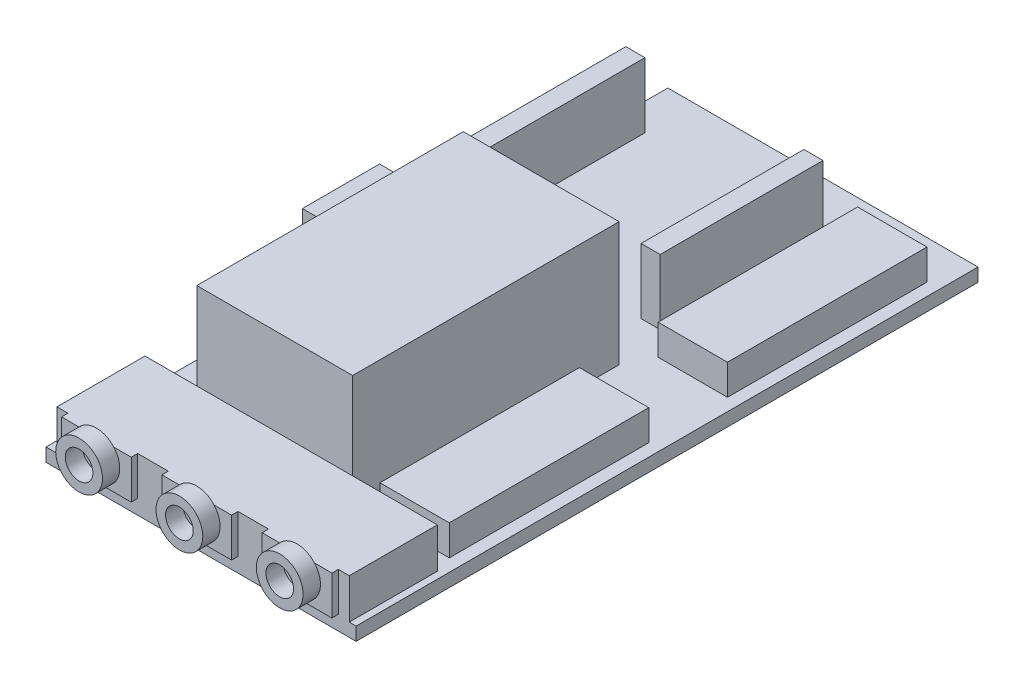
SolidWorks part; units mm, degrees
ref_plane "Front Plane" through (0, 0, 0) normal (0, 0, 1) x (1, 0, 0)
ref_plane "Top Plane" through (0, 0, 0) normal (0, 1, 0) x (1, 0, 0)
ref_plane "Right Plane" through (0, 0, 0) normal (1, 0, 0) x (0, 0, -1)
sketch "Sketch1" plane through (0, 0, 0) normal (0, 1, 0) x (1, 0, 0)
  line L1 (-19.9, -39.9) -> (19.9, -39.9)
  line L2 (-19.9, -39.9) -> (-19.9, 39.9)
  line L3 (-19.9, 39.9) -> (19.9, 39.9)
  line L4 (19.9, -39.9) -> (19.9, 39.9)
  line L5 (-19.9, -39.9) -> (19.9, 39.9) construction
  line L6 (-19.9, 39.9) -> (19.9, -39.9) construction
  point P0 (0, 0)
  dimension "D1" = 39.8
  dimension "D2" = 79.8
extrude "Boss-Extrude1" add sketch "Sketch1" along normal blind 1.7
sketch "Sketch2" plane through (0, 1.7, 0) normal (0, 1, 0) x (1, 0, 0)
  line L0 (-19.9, 39.9) -> (-19.9, -39.9) construction
  line L1 (-12.27, -28.18) -> (7.73, -28.18)
  line L2 (-12.27, -28.18) -> (-12.27, 6.02)
  line L3 (-12.27, 6.02) -> (7.73, 6.02)
  line L4 (7.73, -28.18) -> (7.73, 6.02)
  line L5 (-12.27, -28.18) -> (7.73, 6.02) construction
  line L6 (-12.27, 6.02) -> (7.73, -28.18) construction
  line L7 (19.9, 39.9) -> (-19.9, 39.9) construction
  point P0 (-2.27, -11.08)
  dimension "D1" = 34.2
  dimension "D2" = 20
  dimension "D3" = 7.63
  dimension "D4" = 33.88
extrude "Boss-Extrude2" add sketch "Sketch2" along normal blind 15.9
sketch "Sketch3" plane through (0, 1.7, 0) normal (0, 1, 0) x (1, 0, 0)
  line L0 (-19.9, 39.9) -> (-19.9, -39.9) construction
  line L1 (-18.84, 12.55) -> (-16.39, 12.55)
  line L2 (-18.84, 12.55) -> (-18.84, 33.45)
  line L3 (-18.84, 33.45) -> (-16.39, 33.45)
  line L4 (-16.39, 12.55) -> (-16.39, 33.45)
  line L5 (4.01, 12.55) -> (6.46, 12.55)
  line L6 (4.01, 12.55) -> (4.01, 33.45)
  line L7 (4.01, 33.45) -> (6.46, 33.45)
  line L8 (6.46, 12.55) -> (6.46, 33.45)
  line L9 (19.9, 39.9) -> (-19.9, 39.9) construction
  dimension "D1" = 20.9
  dimension "D2" = 2.45
  dimension "D3" = 2.45
  dimension "D4" = 20.4
  dimension "D5" = 1.06
  dimension "D6" = 6.45
extrude "Boss-Extrude3" add sketch "Sketch3" along normal blind 8.35
sketch "Sketch4" plane through (0, 1.7, 0) normal (0, 1, 0) x (1, 0, 0)
  line L1 (-19.9, -7) -> (-12.27, -7)
  line L2 (-19.9, -7) -> (-19.9, 2.9)
  line L3 (-19.9, 2.9) -> (-12.27, 2.9)
  line L4 (-12.27, -7) -> (-12.27, 2.9)
  line L5 (-19.9, 39.9) -> (-19.9, -39.9) construction
  line L6 (-12.27, 6.02) -> (-12.27, -28.18) construction
  line L7 (19.9, 39.9) -> (-19.9, 39.9) construction
  dimension "D1" = 9.9
  dimension "D2" = 37
extrude "Boss-Extrude4" add sketch "Sketch4" along normal blind 10.05
sketch "Sketch5" plane through (0, 1.7, 0) normal (0, 1, 0) x (1, 0, 0)
  line L0 (19.9, 39.9) -> (-19.9, 39.9) construction
  line L1 (9.4, -26.35) -> (18.3, -26.35)
  line L2 (9.4, -26.35) -> (9.4, -0.75)
  line L3 (9.4, -0.75) -> (18.3, -0.75)
  line L4 (18.3, -26.35) -> (18.3, -0.75)
  line L5 (9.4, 9.35) -> (18.3, 9.35)
  line L6 (9.4, 9.35) -> (9.4, 34.95)
  line L7 (9.4, 34.95) -> (18.3, 34.95)
  line L8 (18.3, 9.35) -> (18.3, 34.95)
  line L9 (19.9, -39.9) -> (19.9, 39.9) construction
  dimension "D1" = 8.9
  dimension "D2" = 25.6
  dimension "D3" = 10.1
  dimension "D4" = 4.95
  dimension "D5" = 25.6
  dimension "D6" = 1.6
extrude "Boss-Extrude5" add sketch "Sketch5" along normal blind 3.9
sketch "Sketch6" plane through (0, 1.7, 0) normal (0, 1, 0) x (1, 0, 0)
  line L0 (-19.9, -7) -> (-19.9, -39.9) construction
  line L1 (-18.5, -28.6) -> (19.02, -28.6)
  line L2 (-18.5, -28.6) -> (-18.5, -39.9)
  line L3 (-18.5, -39.9) -> (19.02, -39.9)
  line L4 (19.02, -28.6) -> (19.02, -39.9)
  line L5 (19.9, -39.9) -> (19.9, 39.9) construction
  line L6 (-19.9, -39.9) -> (19.9, -39.9) construction
  dimension "D1" = 37.52
  dimension "D2" = 1.4
  dimension "D3" = 0.88
  dimension "D4" = 11.3
extrude "Boss-Extrude6" add sketch "Sketch6" along normal blind 5.16
sketch "Sketch7" plane through (0, 0, 39.9) normal (0, 0, 1) x (1, 0, 0)
  line L0 (-18.5, 6.86) -> (19.02, 6.86) construction
  line L1 (-4.215, 1.86) -> (4.735, 1.86)
  line L2 (-4.215, 1.86) -> (-4.215, 6.86)
  line L3 (-4.215, 6.86) -> (4.735, 6.86)
  line L4 (4.735, 1.86) -> (4.735, 6.86)
  line L5 (-4.215, 1.86) -> (4.735, 6.86) construction
  line L6 (-4.215, 6.86) -> (4.735, 1.86) construction
  line L7 (-18.5, 4.28) -> (19.02, 4.28) construction
  line L8 (-18.5, 6.86) -> (-18.5, 1.7) construction
  line L9 (19.02, 6.86) -> (19.02, 1.7) construction
  point P0 (0.26, 4.36)
  point P13 (0.26, 4.28)
  dimension "D1" = 5
  dimension "D2" = 8.95
extrude "Boss-Extrude7" add sketch "Sketch7" along normal blind 0.82
sketch "Sketch8" plane through (0, 0, 40.72) normal (0, 0, 1) x (1, 0, 0)
  line L0 (0.26, 1.86) -> (2.5264, 1.86) construction
  line L1 (-4.215, 1.86) -> (4.735, 1.86) construction
  line L2 (0.26, 6.86) -> (0.26, 3.8897) construction
  line L3 (4.735, 6.86) -> (-4.215, 6.86) construction
  circle A0 centre (0.26, 4.86) radius 3
  circle A1 centre (0.26, 4.86) radius 1.775
  dimension "D1" = 6
  dimension "D2" = 3.55
extrude "Boss-Extrude8" add sketch "Sketch8" along normal blind 2.22
pattern_linear "LPattern1" count 2 spacing 12.875 along (-1, 0, 0) of "Boss-Extrude8", "Boss-Extrude7"
pattern_linear "LPattern2" count 2 spacing 12.875 along (1, 0, 0) of "Boss-Extrude8", "Boss-Extrude7"
